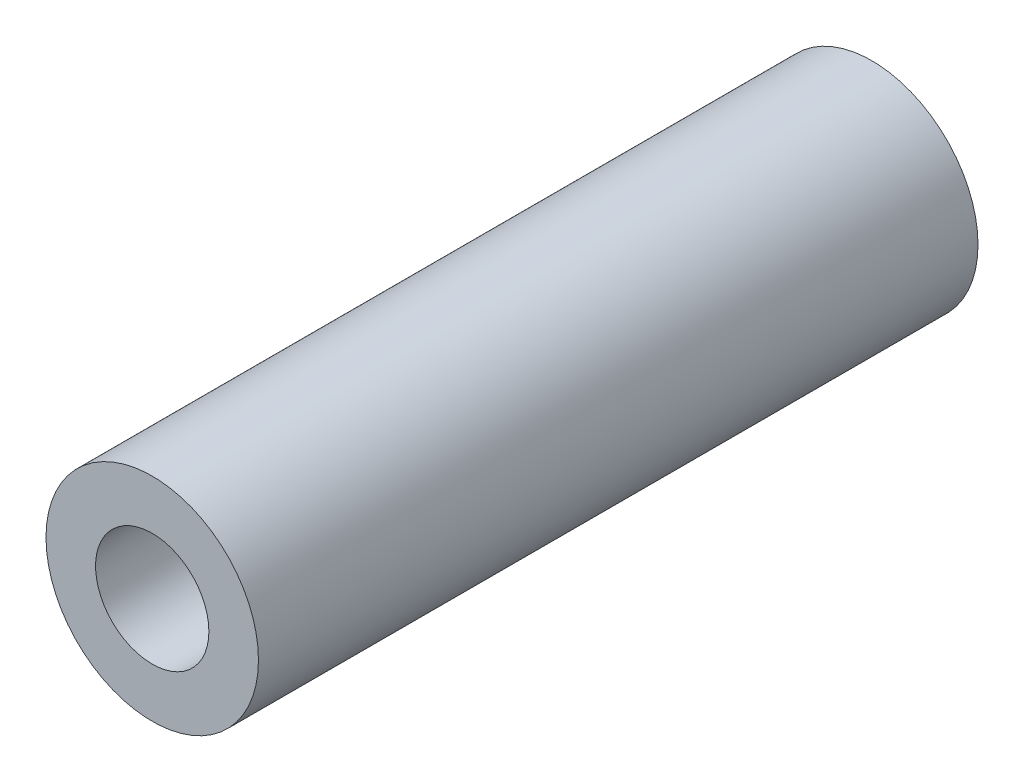
SolidWorks part; units mm, degrees
material "PET"
ref_plane "Front Plane" through (0, 0, 0) normal (0, 0, 1) x (1, 0, 0)
ref_plane "Top Plane" through (0, 0, 0) normal (0, 1, 0) x (1, 0, 0)
ref_plane "Right Plane" through (0, 0, 0) normal (1, 0, 0) x (0, 0, -1)
sketch "Sketch1" plane through (0, 0, 0) normal (0, 0, 1) x (1, 0, 0)
  circle A0 centre (0, 0) radius 2
  circle A1 centre (0, 0) radius 3.75
  dimension "D1" = 4
  dimension "D2" = 7.5
extrude "Boss-Extrude1" add sketch "Sketch1" along normal blind 25.4
